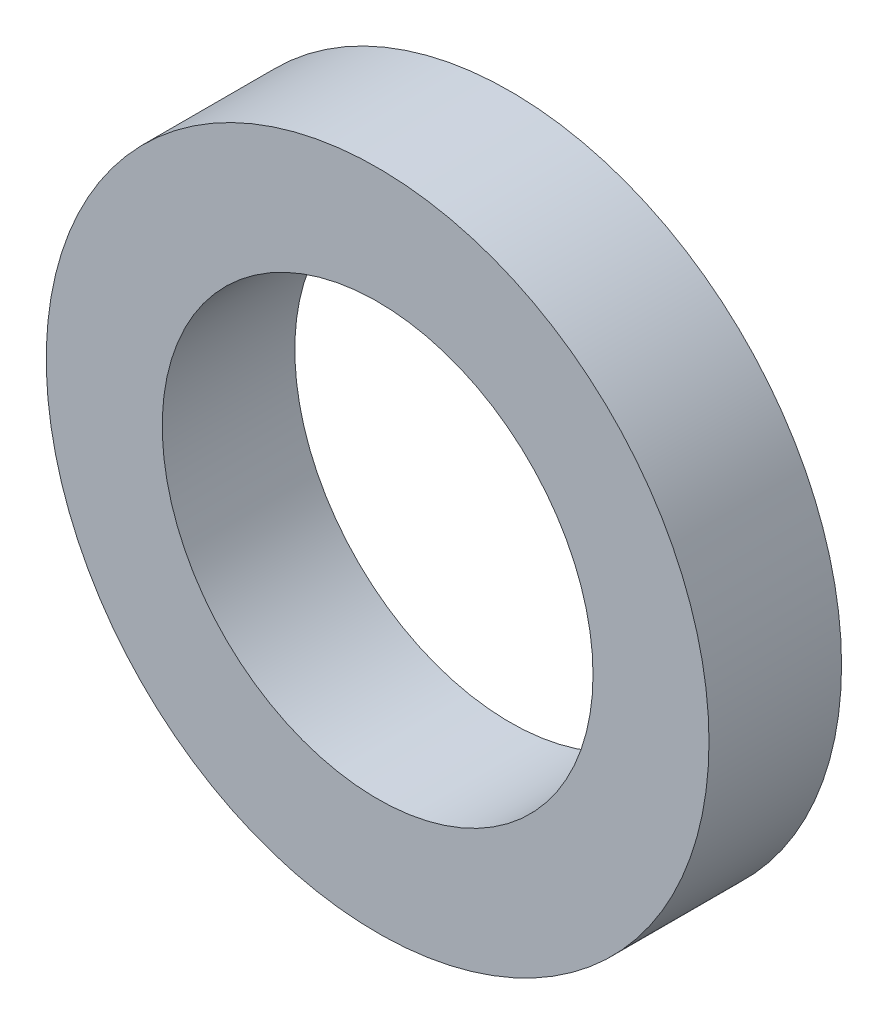
SolidWorks part; units mm, degrees
material "ABS"
ref_plane "正面" through (0, 0, 0) normal (0, 0, 1) x (1, 0, 0)
ref_plane "平面" through (0, 0, 0) normal (0, 1, 0) x (1, 0, 0)
ref_plane "右側面" through (0, 0, 0) normal (1, 0, 0) x (0, 0, -1)
sketch "ｽｹｯﾁ1" plane through (0, 0, 0) normal (0, 0, 1) x (1, 0, 0)
  circle A0 centre (0, 0) radius 3.25
  circle A1 centre (0, 0) radius 5
  dimension "D1" = 6.5
  dimension "D2" = 10
extrude "ﾎﾞｽ - 押し出し1" add sketch "ｽｹｯﾁ1" along normal blind 2
